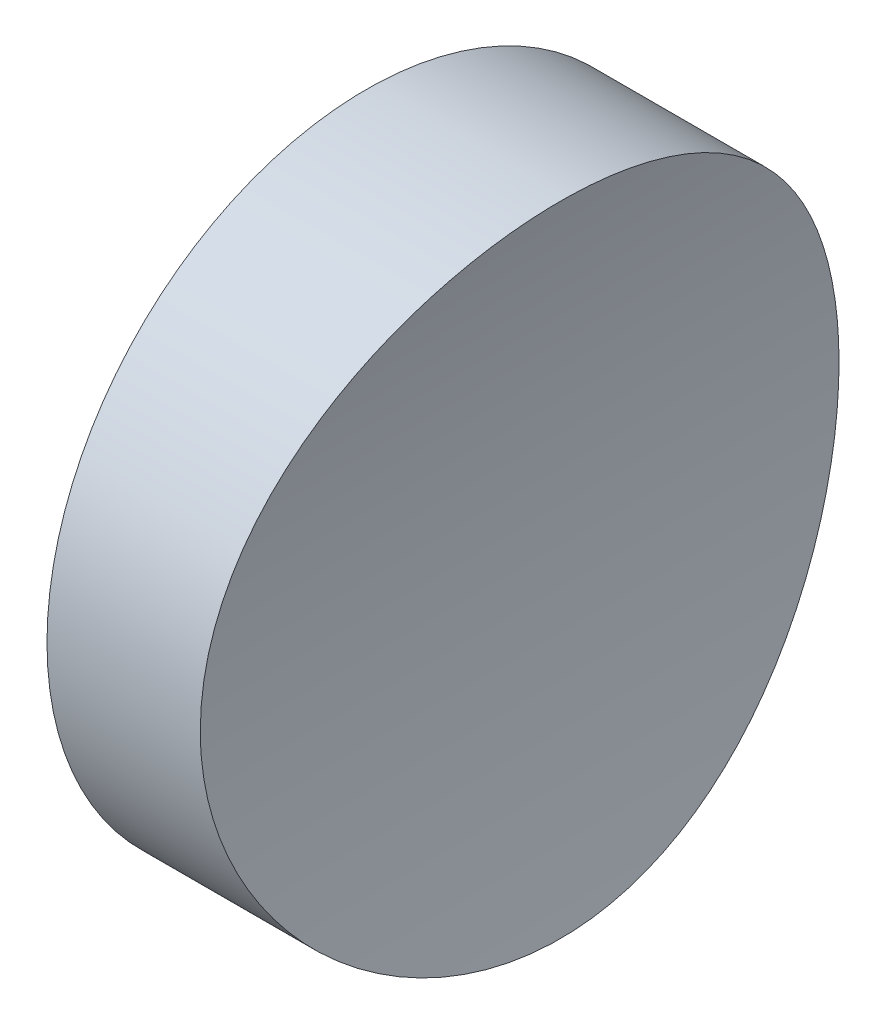
SolidWorks part; units mm, degrees
ref_plane "前视基准面" through (0, 0, 0) normal (0, 0, 1) x (1, 0, 0)
ref_plane "上视基准面" through (0, 0, 0) normal (0, 1, 0) x (1, 0, 0)
ref_plane "右视基准面" through (0, 0, 0) normal (1, 0, 0) x (0, 0, -1)
sketch "草图1" plane through (0, 0, 0) normal (1, 0, 0) x (0, 0, -1)
  circle A0 centre (0, 0) radius 12.5
  dimension "D1" = 25
extrude "凸台-拉伸1" add sketch "草图1" along normal blind 10
sketch "草图2" plane through (0, 0, 0) normal (0, 0, 1) x (1, 0, 0)
  line L0 (0, 0) -> (56, 0) construction
  line L1 (0, 0) -> (6, 0) construction
  circle A0 centre (56, 0) radius 50
  dimension "D1" = 100
  dimension "D2" = 6
extrude "切除-拉伸1" cut sketch "草图2" against normal through all both and the other way through all
